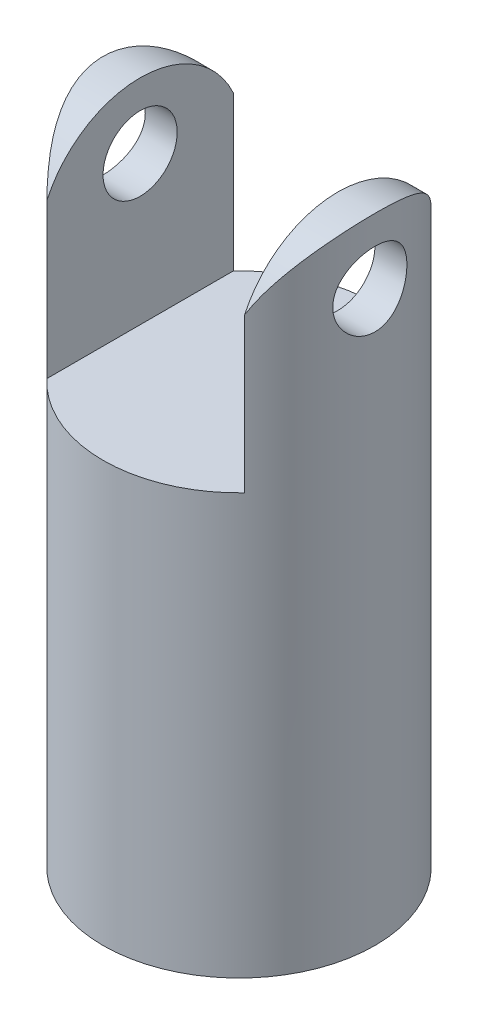
SolidWorks part; units mm, degrees
ref_plane "前视基准面" through (0, 0, 0) normal (0, 0, 1) x (1, 0, 0)
ref_plane "上视基准面" through (0, 0, 0) normal (0, 1, 0) x (1, 0, 0)
ref_plane "右视基准面" through (0, 0, 0) normal (1, 0, 0) x (0, 0, -1)
sketch "草图1" plane through (0, 0, 0) normal (0, 1, 0) x (1, 0, 0)
  circle A0 centre (0, 0) radius 5.5
  dimension "D1" = 11
extrude "凸台-拉伸1" add sketch "草图1" along normal blind 26
sketch "草图2" plane through (0, 0, 0) normal (0, 0, 1) x (1, 0, 0)
  line L0 (5.5, 26) -> (-5.5, 26) construction
  line L1 (-4, 35) -> (4, 35)
  line L2 (-4, 35) -> (-4, 17)
  line L3 (-4, 17) -> (4, 17)
  line L4 (4, 35) -> (4, 17)
  line L5 (-4, 35) -> (4, 17) construction
  line L6 (-4, 17) -> (4, 35) construction
  line L7 (5.5, 0) -> (5.5, 26) construction
  point P0 (0, 26)
  dimension "D1" = 9
  dimension "D2" = 1.5
extrude "切除-拉伸1" cut sketch "草图2" against normal mid plane 50
sketch "草图3" plane through (-4, 0, 0) normal (1, 0, 0) x (0, 0, -1)
  line L0 (3.7749, 26) -> (-3.7749, 26) construction
  circle A0 centre (0, 23) radius 1.5
  dimension "D1" = 3
  dimension "D2" = 3
extrude "切除-拉伸2" cut sketch "草图3" against normal mid plane 50
sketch "草图5" plane through (0, 0, 0) normal (1, 0, 0) x (0, 0, -1)
  line L1 (-4.1533, 21.5) -> (-12.2151, 24.9183)
  line L2 (-12.2151, 24.9183) -> (0.6299, 32.7807)
  line L3 (0.6299, 32.7807) -> (12.9914, 24.5987)
  line L4 (12.9914, 24.5987) -> (4.1533, 21.5)
  arc A0 (4.1533, 21.5) -> (-4.1533, 21.5) centre (0, 21.5) ccw
  circle A1 centre (0, 23) radius 1.5 construction
extrude "切除-拉伸3" cut sketch "草图5" against normal mid plane 22
